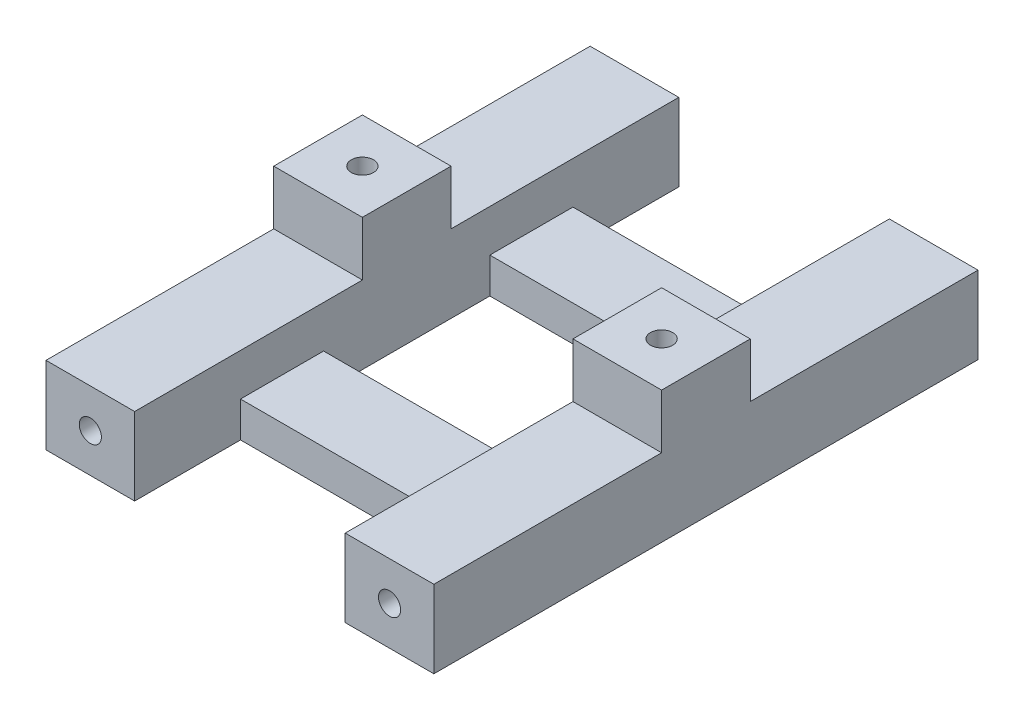
SolidWorks part; units mm, degrees
ref_plane "Alzado" through (0, 0, 0) normal (0, 0, 1) x (1, 0, 0)
ref_plane "Planta" through (0, 0, 0) normal (0, 1, 0) x (1, 0, 0)
ref_plane "Vista lateral" through (0, 0, 0) normal (1, 0, 0) x (0, 0, -1)
sketch "Croquis1" plane through (0, 0, 0) normal (0, 1, 0) x (1, 0, 0)
  line L0 (-10.4076, 7.3865) -> (8.5924, 7.3865)
  line L1 (-10.4076, 7.3865) -> (-10.4076, -7.6135)
  line L2 (-10.4076, -7.6135) -> (8.5924, -7.6135)
  line L3 (8.5924, 7.3865) -> (8.5924, -7.6135)
  line L4 (16.5924, -24.6635) -> (16.5924, 24.4365)
  line L5 (16.5924, 24.4365) -> (8.5924, 24.4365)
  line L6 (8.5924, 24.4365) -> (8.5924, 14.8865)
  line L7 (8.5924, 14.8865) -> (-10.4076, 14.8865)
  line L8 (-10.4076, 14.8865) -> (-10.4076, 24.4365)
  line L9 (-10.4076, 24.4365) -> (-18.4076, 24.4365)
  line L10 (-18.4076, 24.4365) -> (-18.4076, -24.6635)
  line L11 (-18.4076, -24.6635) -> (-10.4076, -24.6635)
  line L12 (-10.4076, -24.6635) -> (-10.4076, -15.1135)
  line L13 (-10.4076, -15.1135) -> (8.5924, -15.1135)
  line L14 (8.5924, -15.1135) -> (8.5924, -24.6635)
  line L15 (8.5924, -24.6635) -> (16.5924, -24.6635)
extrude "Saliente-Extruir1" add sketch "Croquis1" along normal blind 7
sketch "Croquis2" plane through (0, 7, 0) normal (0, 1, 0) x (1, 0, 0)
  line L0 (-18.4076, 24.4365) -> (-18.4076, -24.6635) construction
  line L1 (-18.4076, 3.8865) -> (-10.4076, 3.8865)
  line L2 (-18.4076, 3.8865) -> (-18.4076, -4.1135)
  line L3 (-18.4076, -4.1135) -> (-10.4076, -4.1135)
  line L4 (-10.4076, 3.8865) -> (-10.4076, -4.1135)
  line L5 (-10.4076, 7.3865) -> (-10.4076, -7.6135) construction
  line L6 (8.5924, -7.6135) -> (8.5924, 7.3865) construction
  line L7 (8.5924, 3.8865) -> (16.5924, 3.8865)
  line L8 (8.5924, 3.8865) -> (8.5924, -4.1135)
  line L9 (8.5924, -4.1135) -> (16.5924, -4.1135)
  line L10 (16.5924, 3.8865) -> (16.5924, -4.1135)
  line L11 (16.5924, -24.6635) -> (16.5924, 24.4365) construction
  circle A0 centre (-14.4076, -0.1135) radius 1
  circle A1 centre (12.5924, -0.1135) radius 1
  point P16 (-10.4076, -0.1135)
  point P17 (-18.4076, -0.1135)
  point P22 (12.5924, 3.8865)
  point P23 (-14.4076, 3.8865)
  point P24 (0, 0)
  dimension "D2" = 2
  dimension "D1" = 8
extrude "Saliente-Extruir2" add sketch "Croquis2" along normal blind 4.9
sketch "Croquis3" plane through (0, 0, 15.1135) normal (0, 0, 1) x (1, 0, 0)
  line L1 (-10.4076, 7) -> (8.5924, 7)
  line L2 (-10.4076, 7) -> (-10.4076, 3.2)
  line L3 (-10.4076, 3.2) -> (8.5924, 3.2)
  line L4 (8.5924, 7) -> (8.5924, 3.2)
  dimension "D1" = 3.8
extrude "Cortar-Extruir1" cut sketch "Croquis3" against normal blind 37.9
sketch "Croquis4" plane through (0, 0, 24.6635) normal (0, 0, 1) x (1, 0, 0)
  line L0 (-18.4076, 0) -> (-10.4076, 0) construction
  line L1 (8.5924, 0) -> (16.5924, 0) construction
  line L2 (-18.4076, 7) -> (-18.4076, 0) construction
  circle A0 centre (12.5924, 3.5) radius 1
  circle A1 centre (-14.4076, 3.5) radius 1
  point P4 (0, 0)
  point P5 (0, 0)
  point P8 (-14.4076, 0)
  point P9 (0, 0)
  point P12 (12.5924, 0)
  point P15 (-18.4076, 3.5)
  point P16 (0, 0)
  dimension "D1" = 2
extrude "Cortar-Extruir2" cut sketch "Croquis4" against normal blind 51.9
